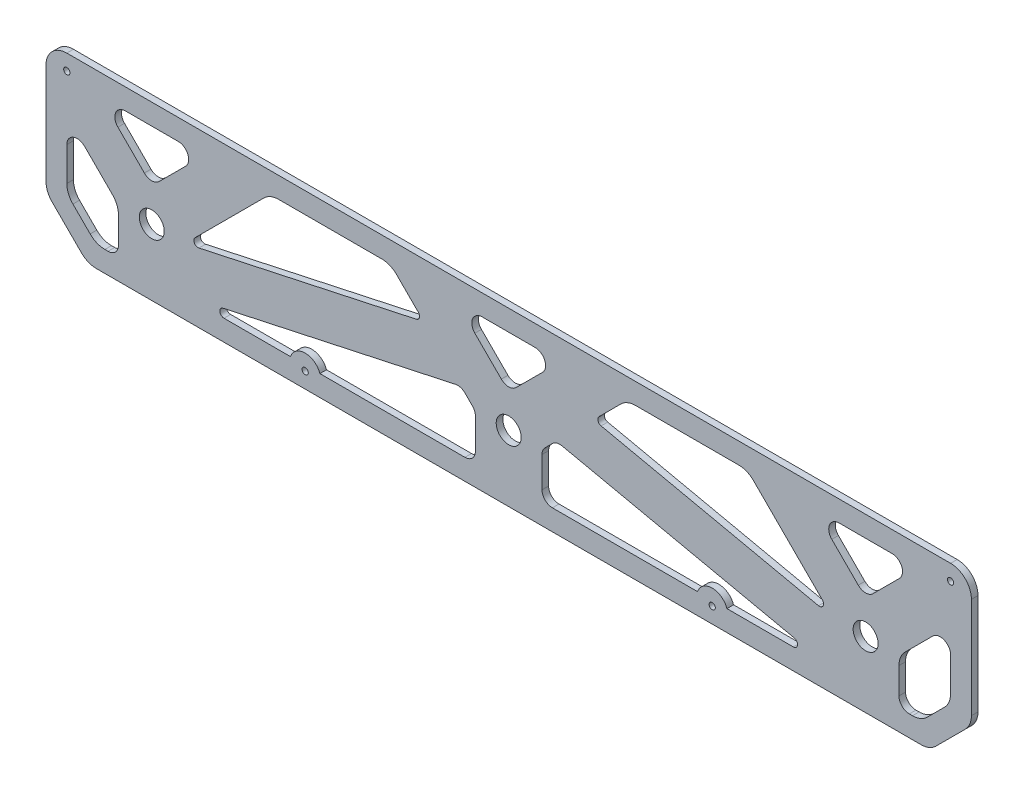
SolidWorks part; units mm, degrees
ref_plane "Front Plane" through (0, 0, 0) normal (0, 0, 1) x (1, 0, 0)
ref_plane "Top Plane" through (0, 0, 0) normal (0, 1, 0) x (1, 0, 0)
ref_plane "Right Plane" through (0, 0, 0) normal (1, 0, 0) x (0, 0, -1)
sketch "Sketch1" plane through (0, 0, 0) normal (0, 0, 1) x (1, 0, 0)
  line L0 (2.9289, 17.0711) -> (17.0711, 2.9289)
  line L1 (24.1421, 0) -> (420.3579, 0)
  line L2 (0, 24.1421) -> (0, 72.55)
  line L3 (10, 82.55) -> (434.5, 82.55)
  line L4 (444.5, 24.1421) -> (444.5, 72.55)
  line L5 (427.4289, 2.9289) -> (441.5711, 17.0711)
  line L6 (10, 28.2843) -> (10, 56.5504)
  line L7 (25.9996, 72.55) -> (75.6004, 72.55)
  line L8 (434.5, 28.2843) -> (434.5, 62.55)
  line L9 (423.2868, 12.9289) -> (431.5711, 21.2132)
  line L10 (28.2843, 10) -> (34.8004, 10)
  line L11 (12.9289, 21.2132) -> (21.2132, 12.9289)
  line L12 (222.25, 82.55) -> (222.25, 25.75) construction
  line L13 (0, 82.55) -> (444.5, 82.55) construction
  line L14 (444.5, 20) -> (444.5, 82.55) construction
  line L15 (0, 20) -> (0, 82.55) construction
  line L16 (10, 72.55) -> (434.5, 72.55) construction
  line L17 (434.5, 24.1421) -> (434.5, 72.55) construction
  line L18 (10, 24.1421) -> (10, 72.55) construction
  line L19 (420.3579, 10) -> (434.5, 24.1421) construction
  line L20 (24.1421, 10) -> (420.3579, 10) construction
  line L21 (10, 24.1421) -> (24.1421, 10) construction
  line L22 (0, 20) -> (20, 0) construction
  line L23 (20, 0) -> (424.5, 0) construction
  line L24 (424.5, 0) -> (444.5, 20) construction
  line L25 (34.8004, 31.75) -> (34.8004, 10)
  line L26 (409.6996, 10) -> (416.2157, 10)
  line L27 (206.25, 31.75) -> (206.25, 10)
  line L28 (238.25, 31.75) -> (238.25, 10)
  line L29 (66.7996, 10) -> (117.4168, 10)
  line L30 (409.6996, 31.75) -> (409.6996, 10)
  line L31 (222.25, 47.75) -> (197.45, 72.55)
  line L32 (206.25, 31.75) -> (199.3315, 38.6685)
  line L33 (222.25, 47.75) -> (247.05, 72.55)
  line L34 (238.25, 31.75) -> (245.1685, 38.6685)
  line L35 (197.45, 72.55) -> (247.05, 72.55)
  line L36 (279.05, 72.55) -> (336.9004, 72.55)
  line L37 (66.7996, 31.75) -> (107.5996, 72.55)
  line L38 (34.8004, 31.75) -> (10, 56.5504)
  line L39 (50.8, 47.7496) -> (25.9996, 72.55)
  line L40 (50.8, 47.7496) -> (75.6004, 72.55)
  line L41 (131.5589, 10) -> (206.25, 10)
  line L42 (409.6996, 31.75) -> (434.5, 56.5504)
  line L43 (393.7, 47.7496) -> (418.5004, 72.55)
  line L44 (393.7, 47.7496) -> (368.8996, 72.55)
  line L45 (377.7004, 31.75) -> (336.9004, 72.55)
  line L46 (66.7996, 31.75) -> (181.4496, 56.5504)
  line L47 (66.7996, 10) -> (199.3315, 38.6685)
  line L48 (377.7004, 10) -> (245.1685, 38.6685)
  line L49 (377.7004, 31.75) -> (263.0504, 56.5504)
  line L50 (181.4496, 56.5504) -> (165.45, 72.55)
  line L51 (263.0504, 56.5504) -> (279.05, 72.55)
  line L52 (238.25, 10) -> (312.9411, 10)
  line L53 (107.5996, 72.55) -> (165.45, 72.55)
  line L54 (368.8996, 72.55) -> (418.5004, 72.55)
  line L55 (327.0832, 10) -> (377.7004, 10)
  circle A0 centre (50.8, 31.75) radius 5.9996
  circle A1 centre (393.7, 31.75) radius 5.9996
  circle A2 centre (222.25, 31.75) radius 6
  arc A3 (434.5, 82.55) -> (444.5, 72.55) centre (434.5, 72.55) cw
  arc A4 (0, 72.55) -> (10, 82.55) centre (10, 72.55) cw
  arc A7 (434.5, 28.2843) -> (431.5711, 21.2132) centre (424.5, 28.2843) cw
  arc A8 (423.2868, 12.9289) -> (416.2157, 10) centre (416.2157, 20) cw
  arc A9 (10, 28.2843) -> (12.9289, 21.2132) centre (20, 28.2843) ccw
  arc A10 (28.2843, 10) -> (21.2132, 12.9289) centre (28.2843, 20) cw
  arc A11 (17.0711, 2.9289) -> (24.1421, 0) centre (24.1421, 10) ccw
  arc A12 (2.9289, 17.0711) -> (0, 24.1421) centre (10, 24.1421) cw
  arc A13 (441.5711, 17.0711) -> (444.5, 24.1421) centre (434.5, 24.1421) ccw
  arc A14 (427.4289, 2.9289) -> (420.3579, 0) centre (420.3579, 10) cw
  circle A18 centre (10, 75.05) radius 1.5
  circle A19 centre (434.5, 75.05) radius 1.5
  circle A21 centre (124.4878, 7.5) radius 1.5
  arc A22 (131.5589, 10) -> (117.4168, 10) centre (124.4878, 7.5) ccw
  arc A23 (312.9411, 10) -> (327.0832, 10) centre (320.0122, 7.5) cw
  circle A24 centre (320.0122, 7.5) radius 1.5
  point P0 (0, 0)
  point P3 (444.5, 0)
  point P15 (24.1421, 24.1421)
  point P16 (17.0711, 17.0711)
  point P17 (427.4289, 17.0711)
  point P18 (420.3579, 24.1421)
  point P54 (20, 0)
  point P75 (124.4878, 0)
  point P76 (222.25, 10)
  point P77 (222.25, 10)
  point P78 (320.0122, 0)
  point P79 (222.25, 10)
  point P104 (320.0122, 7.5)
  dimension "D4" = 31.75
  dimension "D6" = 10
  dimension "D1" = 10
  dimension "D9" = 10
  dimension "D12" = 7.5
  dimension "D8" = 7.5
  dimension "D2" = 444.5
  dimension "D5" = 50.8
  dimension "D3" = 10
extrude "Boss-Extrude1" add sketch "Sketch1" along normal blind 3.175 contours A14 L5 A13 L4 A3 L3 A4 L2 A12 L0 A11 L1 L41 A22 L29 L47 L32 L27 A19 A18 A2 L44 L54 L43 L37 L53 L50 L46 L49 L51 L36 L45 L31 L35 L33 L40 L39 L7 A0 A1
fillet "Fillet1" radius 10 6 edges at (279.05, 72.55, 1.5875) (165.45, 72.55, 1.5875) (409.6996, 31.75, 1.5875) (336.9004, 72.55, 1.5875) (34.8004, 31.75, 1.5875) (107.5996, 72.55, 1.5875)
fillet "Fillet2" radius 5 8 edges at (199.3315, 38.6685, 1.5875) (245.1685, 38.6685, 1.5875) (238.25, 31.75, 1.5875) (206.25, 31.75, 1.5875) (409.6996, 10, 1.5875) (206.25, 10, 1.5875) (238.25, 10, 1.5875) (34.8004, 10, 1.5875)
fillet "Fillet3" radius 5 3 edges at (197.45, 72.55, 1.5875) (247.05, 72.55, 1.5875) (222.25, 47.75, 1.5875)
fillet "Fillet4" radius 5 8 edges at (434.5, 56.5504, 1.5875) (393.7, 47.7496, 1.5875) (418.5004, 72.55, 1.5875) (368.8996, 72.55, 1.5875) (10, 56.5504, 1.5875) (25.9996, 72.55, 1.5875) (75.6004, 72.55, 1.5875) (50.8, 47.7496, 1.5875)
fillet "Fillet5" radius 2 6 edges at (263.0504, 56.5504, 1.5875) (181.4496, 56.5504, 1.5875) (377.7004, 31.75, 1.5875) (377.7004, 10, 1.5875) (66.7996, 10, 1.5875) (66.7996, 31.75, 1.5875)
sketch "Sketch2" plane through (0, 0, 3.175) normal (0, 0, 1) x (1, 0, 0)
  line L0 (10, 82.55) -> (434.5, 82.55) construction
  line L1 (97.075, 104.55) -> (97.075, 82.55)
  line L2 (135.175, 104.55) -> (135.175, 82.55)
  line L3 (222.25, 82.55) -> (222.25, -13.4544)
  line L4 (309.325, 104.55) -> (309.325, 82.55)
  line L5 (347.425, 104.55) -> (347.425, 82.55)
  line L6 (97.075, 82.55) -> (135.175, 82.55)
  line L7 (347.425, 82.55) -> (309.325, 82.55)
  arc A1 (135.175, 104.55) -> (97.075, 104.55) centre (116.125, 104.55) ccw
  circle A3 centre (116.125, 104.55) radius 10.9982
  circle A6 centre (116.125, 118.5454) radius 1.55
  circle A7 centre (102.1296, 104.55) radius 1.55
  circle A8 centre (116.125, 90.5546) radius 1.55
  circle A9 centre (130.1204, 104.55) radius 1.55
  circle A10 centre (314.3796, 104.55) radius 1.55
  circle A11 centre (328.375, 90.5546) radius 1.55
  circle A12 centre (342.3704, 104.55) radius 1.55
  circle A13 centre (328.375, 118.5454) radius 1.55
  circle A14 centre (328.375, 104.55) radius 10.9982
  arc A15 (309.325, 104.55) -> (347.425, 104.55) centre (328.375, 104.55) cw
  point P2 (222.25, 82.55)
  point P8 (116.125, 82.55)
  point P31 (116.125, 104.55)
  point P37 (328.375, 82.55)
  dimension "D2" = 4
extrude "Boss-Extrude2" add sketch "Sketch2" against normal up to surface (3.175 mm away) contours L2 A1 L1 L6 A9 A8 A7 A6 A3 | A15 L4 L7 L5 A13 A11 A10 A12 A14 up to face at (163.5807, 21.1186, 0)
fillet "Fillet6" radius 10 4 edges at (135.175, 82.55, 1.5875) (97.075, 82.55, 1.5875) (347.425, 82.55, 1.5875) (309.325, 82.55, 1.5875)
sketch "Sketch3" plane through (0, 0, 0) normal (0, 0, -1) x (-1, 0, 0)
  line L0 (-10, 82.55) -> (-87.075, 82.55) construction
  line L1 (-468.2769, 208.4798) -> (-36.1737, 208.4798)
  line L2 (-468.2769, 208.4798) -> (-468.2769, 82.55)
  line L3 (-468.2769, 82.55) -> (-36.1737, 82.55)
  line L4 (-36.1737, 208.4798) -> (-36.1737, 82.55)
  point P4 (-36.1737, 82.55)
extrude "Cut-Extrude1" cut sketch "Sketch3" against normal blind 10
sketch "Sketch4" plane through (0, 0, 3.175) normal (0, 0, 1) x (1, 0, 0)
  line L0 (10, 82.55) -> (434.5, 82.55) construction
  circle A0 centre (116.125, 77.55) radius 1.5
  point P0 (222.25, 82.55)
  point P6 (116.125, 82.55)
  point P9 (328.375, 82.55)
  dimension "D1" = 5
